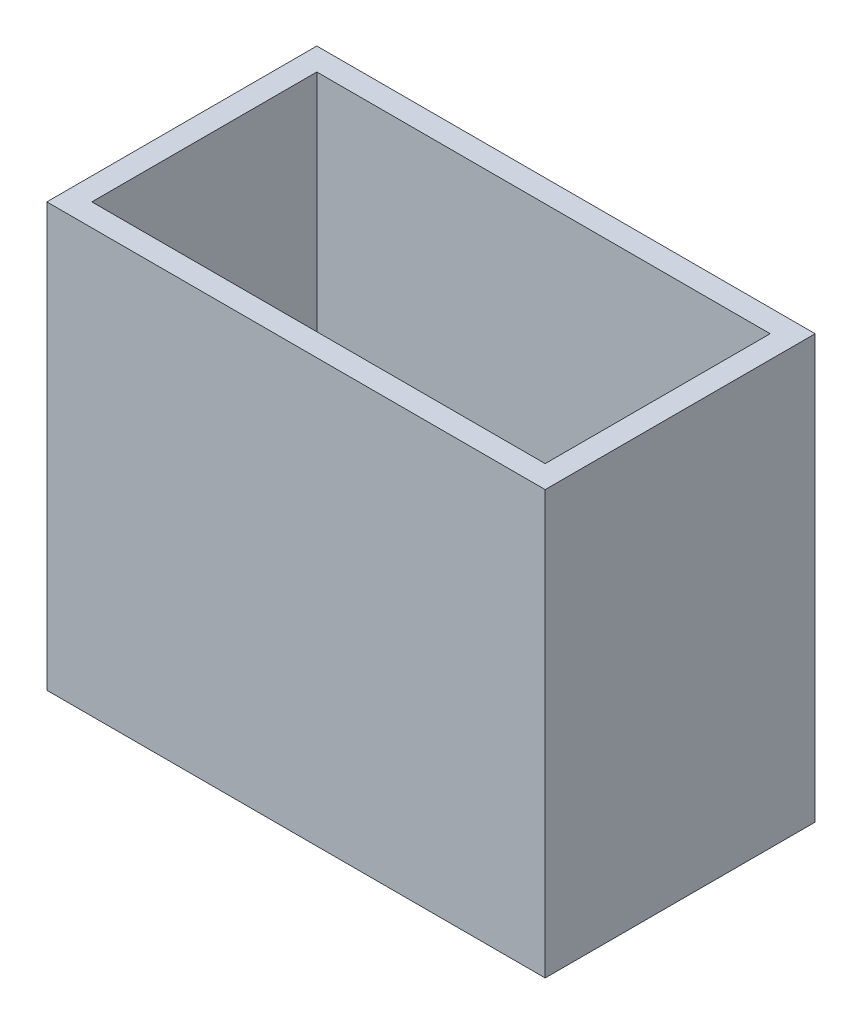
SolidWorks part; units mm, degrees
ref_plane "Front" through (0, 0, 0) normal (0, 0, 1) x (1, 0, 0)
ref_plane "Top" through (0, 0, 0) normal (0, 1, 0) x (1, 0, 0)
ref_plane "Right" through (0, 0, 0) normal (1, 0, 0) x (0, 0, -1)
sketch "草图1" plane through (0, 0, 0) normal (0, 0, 1) x (1, 0, 0)
  line L1 (0, 0) -> (44.3, 0)
  line L2 (0, 0) -> (0, 37.6)
  line L3 (0, 37.6) -> (44.3, 37.6)
  line L4 (44.3, 0) -> (44.3, 37.6)
  dimension "D1" = 44.3
  dimension "D2" = 37.6
extrude "凸台-拉伸1" add sketch "草图1" along normal blind 24
sketch "草图2" plane through (0, 37.6, 0) normal (0, 1, 0) x (1, 0, 0)
  line L0 (0, -24) -> (0, 0) construction
  line L1 (2, -2) -> (42.3, -2)
  line L2 (2, -2) -> (2, -22)
  line L3 (2, -22) -> (42.3, -22)
  line L4 (42.3, -2) -> (42.3, -22)
  line L5 (44.3, -24) -> (44.3, 0) construction
  line L6 (44.3, 0) -> (0, 0) construction
  line L7 (44.3, -24) -> (0, -24) construction
  point P6 (0, -12)
  dimension "D1" = 2
  dimension "D2" = 2
  dimension "D3" = 2
  dimension "D4" = 2
extrude "切除-拉伸1" cut sketch "草图2" against normal blind 36.6
